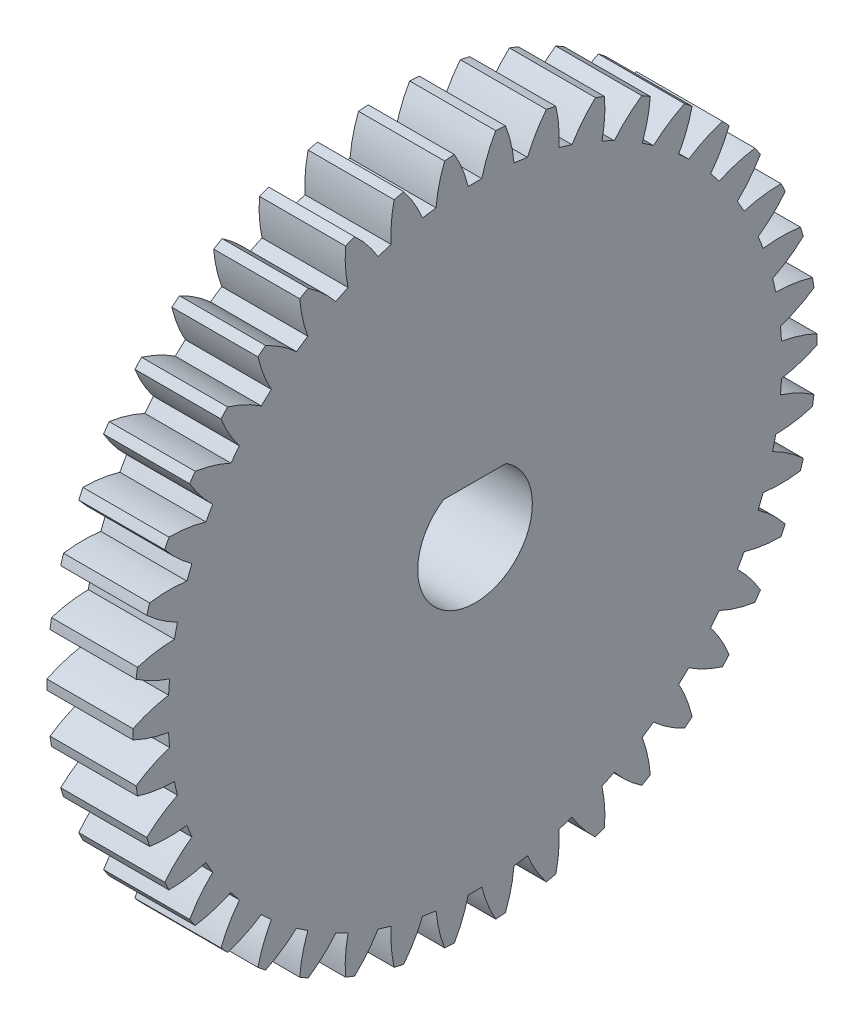
SolidWorks part; units mm, degrees
ref_plane "Plane1" through (0, 0, 0) normal (0, 0, 1) x (1, 0, 0)
ref_plane "Plane2" through (0, 0, 0) normal (0, 1, 0) x (1, 0, 0)
ref_plane "Plane3" through (0, 0, 0) normal (1, 0, 0) x (0, 0, -1)
sketch "HoldingSke" plane through (0, 0, 0) normal (0, 1, 0) x (1, 0, 0)
  line L0 (0, 0) -> (604.0281, -543.8694)
  line L1 (-15, 0) -> (100, 0) construction
  line L2 (0, 0) -> (-2.1039, 2.3779)
  line L3 (0, 0) -> (-11.863, 4.5341)
  line L4 (0, 0) -> (6.4178, 5.7786)
  line L5 (0, 0) -> (-47.5972, -17.7524)
  line L6 (0, 0) -> (-3.6426, -2.4577)
  line L7 (-2.1039, 2.3779) -> (8.8308, 51.9871)
  line L8 (-76.2, 54.61) -> (-75.184, 54.61)
  line L9 (-71.009, 38.7566) -> (-53.1078, 45.2721)
  line L10 (-76.2, 71.12) -> (104.1128, 71.12)
  line L11 (0, 0) -> (-4.3942, 0)
  line L12 (-76.2, 101.6) -> (-76.1716, 101.6)
  line L13 (24.9733, 27.94) -> (52.9518, 28.4284)
  line L14 (24.9733, 27.94) -> (25.0241, 27.9398)
  line L15 (24.9733, 27.94) -> (100.4021, 29.52)
  circle A0 centre (0, 0) radius 0.3969
  circle A1 centre (0, 0) radius 15.6655
  circle A2 centre (0, 0) radius 38.1
  circle A3 centre (0, 0) radius 0.3969
  dimension "MHD" = 31.3309
  dimension "Hub_dia" = 76.2
  dimension "Bore" = 0.7937
  dimension "MBD" = 0.7937
  dimension "Num_teeth" = 42
  dimension "Pitch_radius" = 180.3128
  dimension "Pitch" = 812.8
  dimension "Width" = 4.3942
  dimension "Overall_len" = 50.8
  dimension "Show_teeth" = 42
  dimension "Thickness" = 4.3942
  dimension "OAL" = 50.8001
  dimension "T_dim" = 1.016
  dimension "Ap" = 20
  dimension "H" = 19.05
  dimension "Backlash" = 0.0284
  dimension "Addendum_fac" = 1
  dimension "Dedendum_fac" = 1.2
  dimension "Clearance_fac" = 0.2
  dimension "Dedendum_add" = 0.0508
sketch "BasProSke" plane through (0, 0, 0) normal (0, 1, 0) x (1, 0, 0)
  line L0 (-10, 0) -> (60, 0) construction
  line L1 (0, 0) -> (0, 17.4625)
  line L2 (0, 0) -> (4.3942, 0)
  line L3 (4.3942, 0) -> (4.3942, 17.4625)
  line L4 (4.3942, 17.4625) -> (0, 17.4625)
  dimension "Diameter" = 34.925
  dimension "Thickness" = 4.3942
revolve "Base-Revolve" add sketch "BasProSke" angle 360 about L0
sketch "TooCutSke" plane through (0, 0, 0) normal (1, 0, 0) x (0, 0, -1)
  line L1 (0, 0) -> (0, 107) construction
  line L2 (0, 0) -> (-0.673, 16.6552) construction
  line L3 (0, 0) -> (-2.4898, 33.2246) construction
  line L4 (-0.673, 16.6552) -> (-1.2449, 16.6123) construction
  arc A0 (0.3488, 15.6616) -> (-0.3488, 15.6616) centre (0, 0) ccw
  arc A1 (1.0703, 17.4551) -> (-1.0703, 17.4551) centre (0, 0) ccw
  circle A2 centre (0, 0) radius 16.6687 construction
  circle A3 centre (0, 0) radius 15.6635 construction
  arc A4 (-0.3488, 15.6616) -> (-1.0703, 17.4551) centre (-6.8299, 14.096) ccw
  arc A5 (1.0703, 17.4551) -> (0.3488, 15.6616) centre (6.8299, 14.096) ccw
  dimension "Root_dia" = 31.3309
  dimension "Overcut_dia" = 34.9758
  dimension "Pitch_dia" = 33.3375
  dimension "Base_dia" = 31.327
  dimension "Flank_rad" = 6.6675
  dimension "Half_ang" = 4.286
  dimension "Half_CT" = 0.5735
extrude "ToothCut" cut sketch "TooCutSke" along normal through all
fillet "Breaks" [suppressed] radius 0.0159
fillet "RootFillets" [suppressed] radius 0.2095
pattern_circular "TeethCuts" count 42 every 8.571 about axis through (-10, 0, 0) along (1, 0, 0) of "ToothCut", "RootFillets", "Breaks"
sketch "HubNeaOneSke" plane through (0, 0, 0) normal (-1, 0, 0) x (0, 0, 1)
  circle A0 centre (0, 0) radius 15.6655
  dimension "Diameter" = 31.3309
extrude "HubNearOne" [suppressed] add sketch "HubNeaOneSke" along normal blind 46.4059
sketch "HubNeaBotSke" plane through (0, 0, 0) normal (-1, 0, 0) x (0, 0, 1)
  circle A0 centre (0, 0) radius 15.6655
  dimension "Diameter" = 31.3309
extrude "HubNearBoth" [suppressed] add sketch "HubNeaBotSke" along normal blind 23.2029
ref_plane "FarPln" through (4.3942, 0, 0) normal (1, 0, 0) x (0, 0, -1)
sketch "HubFarSke" plane through (4.3942, 0, 0) normal (1, 0, 0) x (0, 0, -1)
  circle A0 centre (0, 0) radius 15.6655
  dimension "Diameter" = 31.3309
extrude "HubFar" [suppressed] add sketch "HubFarSke" along normal blind 23.2029
sketch "BorSke" plane through (0, 0, 0) normal (1, 0, 0) x (0, 0, -1)
  circle A0 centre (0, 0) radius 0.3969
  dimension "Diameter" = 0.7937
extrude "Bore" cut sketch "BorSke" along normal mid plane 101.6001
sketch "KeySke" plane through (0, 0, 0) normal (1, 0, 0) x (0, 0, -1)
  line L0 (-0.127, 0) -> (-0.127, 0.6191)
  line L1 (-0.127, 0.6191) -> (0.127, 0.6191)
  line L2 (0.127, 0.6191) -> (0.127, 0)
  line L3 (0, 0) -> (0, 34) construction
  line L4 (-0.127, 0) -> (0.127, 0)
  dimension "Offset" = 0.6191
  dimension "Width" = 0.254
extrude "Keyway" [suppressed] cut sketch "KeySke" along normal mid plane 101.6001
pattern_circular "Keyway2" [suppressed] count 2 every 90 about axis through (-10, 0, 0) along (1, 0, 0)
sketch "Sketch1" plane through (4.3942, 0, 0) normal (1, 0, 0) x (0, 0, -1)
  line L0 (-1.5979, 2.45) -> (1.5979, 2.45)
  arc A0 (-1.5979, 2.45) -> (1.5979, 2.45) centre (0, 0) ccw
  dimension "D1" = 5.85
  dimension "D2" = 2.45
extrude "Cut-Extrude1" cut sketch "Sketch1" against normal blind 7.366
equation "' \"Pitch@HoldingSke\" = 4"
equation "' \"Num_teeth@HoldingSke\" = 12"
equation "' \"Ap@HoldingSke\" =  20"
equation "' \"Width@HoldingSke\" = 0.5"
equation "' \"Hub_dia@HoldingSke\"= 1"
equation "' \"Overall_len@HoldingSke\" = 1.0"
equation "' \"Bore@HoldingSke\" = 0.75"
equation "' \"T_dim@HoldingSke\" = 0.85"
equation "' \"Width@KeySke\" = 0.25"
equation "' \"Show_teeth@HoldingSke\" = 13"
equation "' \"Backlash@HoldingSke\" = 0.009"
equation "' \"Addendum_fac@HoldingSke\" = 1.0"
equation "' \"Dedendum_fac@HoldingSke\" = 1.25"
equation "' \"Dedendum_add@HoldingSke\" = 0.00005"
equation "' \"Clearance_fac@HoldingSke\" = 0.25"
equation "' \"Pitch@HoldingSke\" = 0.5"
equation "' \"Num_teeth@HoldingSke\" = 23"
equation "' \"Show_teeth@HoldingSke\" = 23"
equation "' \"Backlash@HoldingSke\" = 0.0375"
equation "\"Overcut_dia@TooCutSke\" = (\"Num_teeth@HoldingSke\" + 2 * \"Addendum_fac@HoldingSke\") / \"Pitch@HoldingSke\" + 0.002"
equation "\"Pitch_dia@TooCutSke\" = \"Num_teeth@HoldingSke\" / \"Pitch@HoldingSke\""
equation "\"Base_dia@TooCutSke\" = \"Num_teeth@HoldingSke\" / \"Pitch@HoldingSke\" * cos((\"Ap@HoldingSke\"  * 3.14159265 / 180))"
equation "\"Root_dia@TooCutSke\" = (\"Num_teeth@HoldingSke\" + 2) / \"Pitch@HoldingSke\" - 2 * (\"Addendum_fac@HoldingSke\" + \"Dedendum_fac@HoldingSke\") / \"Pitch@HoldingSke\" - \"Dedendum_add@HoldingSke\" * 2"
equation "\"Half_ang@TooCutSke\" = 180 / \"Num_teeth@HoldingSke\""
equation "\"Half_CT@TooCutSke\" = \"Num_teeth@HoldingSke\" / \"Pitch@HoldingSke\" * sin((3.14159265 / 2 / \"Num_teeth@HoldingSke\")) / 2 - 7 * \"Backlash@HoldingSke\" / 4"
equation "\"Flank_rad@TooCutSke\" = \"Num_teeth@HoldingSke\" / \"Pitch@HoldingSke\" / 5"
equation "\"Radius@RootFillets\" = \"Clearance_fac@HoldingSke\" / \"Pitch@HoldingSke\" + \"Dedendum_add@HoldingSke\""
equation "\"Break_rad@Breaks\" = 0.02 / \"Pitch@HoldingSke\""
equation "\"Thickness@HoldingSke\" = \"Width@HoldingSke\""
equation "\"OAL@HoldingSke\" = \"Thickness@HoldingSke\""
equation "\"MHD@HoldingSke\" = (\"Num_teeth@HoldingSke\" + 2) / \"Pitch@HoldingSke\" - 2 * (\"Addendum_fac@HoldingSke\" + \"Dedendum_fac@HoldingSke\")  / \"Pitch@HoldingSke\" - \"Dedendum_add@HoldingSke\" * 2"
equation "\"MBD@HoldingSke\" = (\"Num_teeth@HoldingSke\" + 2) / \"Pitch@HoldingSke\" - 2 * (\"Addendum_fac@HoldingSke\" + \"Dedendum_fac@HoldingSke\")  / \"Pitch@HoldingSke\" - \"Dedendum_add@HoldingSke\" * 2 - 0.002"
equation "\"MHD@HoldingSke\" = ((sgn( \"MHD@HoldingSke\" - \"Hub_dia@HoldingSke\" )-1)*( \"MHD@HoldingSke\" - \"Hub_dia@HoldingSke\" ))/-2+ \"Hub_dia@HoldingSke\""
equation "\"MBD@HoldingSke\" = ((sgn( \"MBD@HoldingSke\" - \"Bore@HoldingSke\" )-1)*( \"MBD@HoldingSke\" - \"Bore@HoldingSke\" ))/-2+ \"Bore@HoldingSke\""
equation "\"OAL@HoldingSke\" = ((sgn( \"OAL@HoldingSke\" - \"Overall_len@HoldingSke\" )+1)*( \"OAL@HoldingSke\" - \"Overall_len@HoldingSke\" ))/2 + \"Overall_len@HoldingSke\" + 0.000002"
equation "\"Num_teeth@TeethCuts\" = int( \"Show_teeth@HoldingSke\" ) + 1"
equation "\"Num_teeth@TeethCuts\" = ((sgn( \"Num_teeth@TeethCuts\" - \"Num_teeth@HoldingSke\" )-1)*( \"Num_teeth@TeethCuts\" - \"Num_teeth@HoldingSke\" ))/-2+ \"Num_teeth@HoldingSke\""
equation "\"Num_teeth@TeethCuts\" = ((sgn( \"Num_teeth@TeethCuts\" - 2.0)+1)*( \"Num_teeth@TeethCuts\" - 2.0))/2 +2.0"
equation "\"Angle@TeethCuts\" = 360.0 / \"Num_teeth@HoldingSke\""
equation "\"Diameter@BasProSke\" = (\"Num_teeth@HoldingSke\" + 2 * \"Addendum_fac@HoldingSke\") / \"Pitch@HoldingSke\""
equation "\"Thickness@BasProSke\"  = \"Thickness@HoldingSke\""
equation "' \"Fillet_rad@BasProSke\" =  \"Thickness@HoldingSke\" * 0.05"
equation "\"MHD@HoldingSke\" = ((sgn( \"MHD@HoldingSke\" - \"Root_dia@TooCutSke\" )-1)*( \"MHD@HoldingSke\" - \"Root_dia@TooCutSke\" ))/-2+ \"Root_dia@TooCutSke\""
equation "\"Diameter@HubNeaOneSke\" = \"MHD@HoldingSke\""
equation "\"Length@HubNearOne\" = \"OAL@HoldingSke\" - \"Thickness@BasProSke\""
equation "\"Diameter@HubNeaBotSke\" = \"MHD@HoldingSke\""
equation "\"Length@HubNearBoth\" = ( \"OAL@HoldingSke\" - \"Thickness@BasProSke\" ) / 2.0"
equation "\"Thickness@FarPln\" = \"Thickness@BasProSke\""
equation "\"Diameter@HubFarSke\" = \"MHD@HoldingSke\""
equation "\"Length@HubFar\" = ( \"OAL@HoldingSke\" - \"Thickness@BasProSke\" ) / 2.0"
equation "\"Diameter@BorSke\" = \"MBD@HoldingSke\""
equation "\"D1@Bore\" = \"OAL@HoldingSke\" * 2.0"
equation "\"D1@Keyway\" = \"OAL@HoldingSke\" * 2.0"
equation "\"Offset@KeySke\" = \"T_dim@HoldingSke\" - \"MBD@HoldingSke\" / 2.0"
